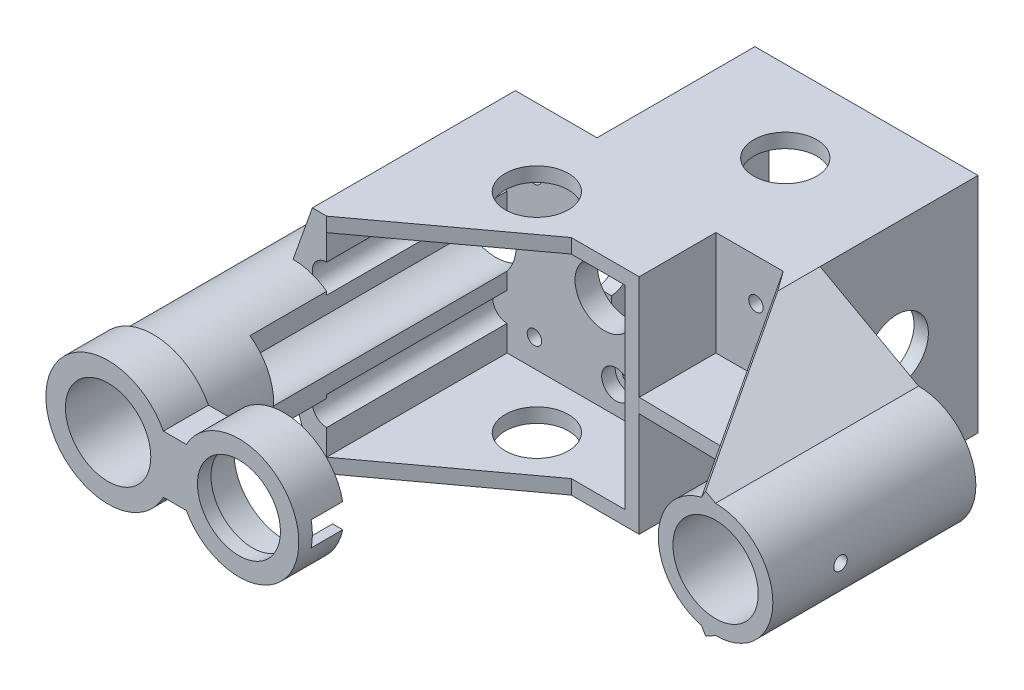
SolidWorks part; units mm, degrees
material "Pure Gold"
ref_plane "Front" through (0, 0, 0) normal (0, 0, 1) x (1, 0, 0)
ref_plane "Top" through (0, 0, 0) normal (0, 1, 0) x (1, 0, 0)
ref_plane "Right" through (0, 0, 0) normal (1, 0, 0) x (0, 0, -1)
sketch "Sketch4" plane through (0, 0, 0) normal (0, 0, 1) x (1, 0, 0)
  line L0 (0, -42.8625) -> (0, 41.275) construction
  line L1 (-49.15, -15.5) -> (-80.15, 15.5) construction
  line L2 (-80.15, -15.5) -> (-49.15, 15.5) construction
  line L3 (-39.925, 44.5615) -> (-39.925, -66.5635) construction
  line L4 (-71.275, 44.5615) -> (-71.275, -66.5635) construction
  line L8 (-62.05, 15.5) -> (-31.05, -15.5) construction
  line L9 (-31.05, 15.5) -> (-62.05, -15.5) construction
  line L11 (-31.05, 36.624) -> (-31.05, -53.8635) construction
  line L12 (43.75, 0) -> (-164.4633, 0) construction
  line L13 (-62.05, 36.624) -> (-62.05, -53.8635) construction
  line L14 (-49.15, 36.624) -> (-49.15, -53.8635) construction
  line L15 (-80.15, 36.624) -> (-80.15, -53.8635) construction
  line L16 (-113.2228, 15.5) -> (-0.2036, 15.5) construction
  line L17 (-113.2228, -15.5) -> (-0.2036, -15.5) construction
  line L18 (-25, -66.5635) -> (-25, 44.5615) construction
  line L19 (-68.1, -66.5635) -> (-68.1, 44.5615) construction
  line L20 (-43.1, 44.5615) -> (-43.1, -66.5635) construction
  line L21 (-86.2, -66.5635) -> (-86.2, 44.5615) construction
  line L22 (5.8397, -21.55) -> (-134.1626, -21.55) construction
  line L23 (5.8397, 21.55) -> (-134.1626, 21.55) construction
  line L24 (10.9249, -24.725) -> (-138.6228, -24.725) construction
  line L25 (10.9249, 24.725) -> (-138.6228, 24.725) construction
  line L26 (-89.375, 44.5615) -> (-89.375, -66.5635) construction
  line L27 (-21.825, 44.5615) -> (-21.825, -66.5635) construction
  circle A0 centre (0, 0) radius 12.7 construction
  circle A1 centre (0, 0) radius 15.875 construction
  circle A2 centre (0, 0) radius 9.46 construction
  circle A3 centre (-93.65, 0) radius 9.46 construction
  arc A4 (-93.65, 12.7) -> (-93.65, -12.7) centre (-93.65, 0) ccw construction
  circle A5 centre (27.27, 0) radius 9.46 construction
  circle A6 centre (27.27, 0) radius 12.7 construction
  circle A7 centre (-120.3675, 0) radius 9.46 construction
  circle A8 centre (-120.3675, 0) radius 12.7 construction
  point P3 (0, 0)
  point P6 (-49.15, -15.5)
  point P11 (-93.65, 0)
  point P12 (-49.15, 15.5)
  point P13 (-46.55, 0)
  point P14 (-80.15, 15.5)
  point P15 (-80.15, -15.5)
  point P61 (-64.65, 0)
  point P65 (27.27, 0)
  point P66 (-120.3675, 0)
  dimension "D20" = 3.175
  dimension "D18" = 29
  dimension "D26" = 73.82
  dimension "D27" = 64.65
  dimension "D2" = 31
  dimension "D3" = 25
  dimension "D4" = 31
  dimension "D5" = 21.825
  dimension "D6" = 15.5
  dimension "D7" = 15.5
  dimension "D8" = 6.05
  dimension "D9" = 6.05
  dimension "D10" = 6.05
  dimension "D11" = 6.05
  dimension "D12" = 6.05
  dimension "D13" = 6.05
  dimension "D14" = 3.175
  dimension "D15" = 3.175
  dimension "D16" = 3.175
  dimension "D17" = 3.175
  dimension "D19" = 3.175
  dimension "D21" = 3.175
  dimension "D22" = 46.55
  dimension "D23" = 47.1
  dimension "D24" = 58.32
  dimension "D25" = 147.6375
sketch "Sketch5" plane through (0, 0, 0) normal (0, 0, 1) x (1, 0, 0)
  line L0 (-21.825, -24.725) -> (0, -12.7)
  line L1 (10.9249, -24.725) -> (-138.6228, -24.725) construction
  line L2 (-21.825, 44.5615) -> (-21.825, -66.5635) construction
  line L3 (0, -42.8625) -> (0, 41.275) construction
  line L4 (10.9249, 24.725) -> (-138.6228, 24.725) construction
  line L5 (-21.825, 24.725) -> (0, 12.7)
  line L6 (-93.65, 0) -> (-93.65, -30.9694) construction
  line L7 (-93.65, 12.7) -> (-89.375, 24.725)
  line L8 (-89.375, 44.5615) -> (-89.375, -66.5635) construction
  line L9 (-89.375, 24.725) -> (-21.825, 24.725)
  line L10 (-89.375, -24.725) -> (-93.65, -12.7)
  line L11 (-89.375, -24.725) -> (-21.825, -24.725)
  circle A0 centre (0, 0) radius 12.7 construction
  arc A1 (0, 12.7) -> (0, -12.7) centre (0, 0) cw
  circle A2 centre (0, 0) radius 9.46
  circle A3 centre (-93.65, 0) radius 9.46
  arc A4 (-93.65, 12.7) -> (-93.65, -12.7) centre (-93.65, 0) ccw
  circle A6 centre (-31.05, 15.5) radius 1.6
  circle A7 centre (-31.05, -15.5) radius 1.6
  circle A8 centre (-49.15, -15.5) radius 1.6
  circle A9 centre (-49.15, 15.5) radius 1.6
  circle A10 centre (-62.05, 15.5) radius 1.6
  circle A11 centre (-80.15, 15.5) radius 1.6
  circle A12 centre (-80.15, -15.5) radius 1.6
  circle A13 centre (-62.05, -15.5) radius 1.6
extrude "Extrude1" add sketch "Sketch5" along normal blind 5
sketch "Sketch6" plane through (0, 0, 5) normal (0, 0, 1) x (1, 0, 0)
  line L0 (-86.2, -21.55) -> (-43.1, -21.55)
  line L1 (-86.2, -66.5635) -> (-86.2, 44.5615) construction
  line L2 (5.8397, -21.55) -> (-134.1626, -21.55) construction
  line L3 (-43.1, 44.5615) -> (-43.1, -66.5635) construction
  line L4 (-43.1, -21.55) -> (-43.1, 21.55)
  line L5 (5.8397, 21.55) -> (-134.1626, 21.55) construction
  line L6 (-43.1, 21.55) -> (-86.2, 21.55)
  line L7 (-39.925, 24.725) -> (-89.375, 24.725)
  line L8 (-93.65, -12.7) -> (-89.375, -24.725) construction
  line L9 (-39.925, 44.5615) -> (-39.925, -66.5635) construction
  line L10 (10.9249, 24.725) -> (-138.6228, 24.725) construction
  line L11 (-12.601, 1.5825) -> (-39.925, 1.5825)
  line L12 (-39.925, -24.725) -> (-89.375, -24.725)
  line L13 (-86.2, 21.55) -> (-86.2, 15.8916)
  line L14 (-86.2, -9.5084) -> (-86.2, -5.83)
  line L15 (-89.375, -24.725) -> (-93.65, -12.7)
  line L16 (-89.375, 24.725) -> (-93.65, 12.7)
  line L19 (-86.2, 9.5416) -> (-86.2, 5.83)
  line L20 (-86.2, -21.55) -> (-86.2, -15.8584)
  line L24 (-39.925, -1.5851) -> (-12.6007, -1.5851)
  line L25 (-39.925, 1.5825) -> (-39.925, 24.725)
  line L27 (-21.825, -24.725) -> (0, -12.7)
  line L28 (-21.825, 24.725) -> (0, 12.7)
  line L29 (-25, 24.725) -> (-3.1127, 12.3127)
  line L30 (-25, -66.5635) -> (-25, 44.5615) construction
  line L31 (-25, -24.725) -> (-3.1127, -12.3127)
  line L32 (10.9249, -24.725) -> (-138.6228, -24.725) construction
  line L33 (-25, -24.725) -> (-21.825, -24.725)
  line L34 (-39.925, -1.5851) -> (-39.925, -24.725)
  line L35 (-25, 24.725) -> (-21.825, 24.725)
  line L36 (0, -42.8625) -> (0, 41.275) construction
  circle A0 centre (-93.65, 0) radius 9.46 construction
  arc A1 (-93.65, 12.7) -> (-93.65, -12.7) centre (-93.65, 0) ccw
  arc A3 (-86.2, 5.83) -> (-86.2, -5.83) centre (-93.65, 0) ccw
  circle A4 centre (0, 0) radius 9.46
  circle A5 centre (0, 0) radius 12.7 construction
  arc A6 (0, -12.7) -> (0, 12.7) centre (0, 0) ccw
  arc A7 (-3.1127, 12.3127) -> (-12.601, 1.5825) centre (0, 0) ccw
  arc A8 (-3.1127, -12.3127) -> (-12.6007, -1.5851) centre (0, 0) cw
  circle A13 centre (-86.2, 12.7166) radius 3.175 construction
  circle A14 centre (-86.2, -12.6834) radius 3.175 construction
  arc A15 (-86.2, 15.8916) -> (-86.2, 9.5416) centre (-86.2, 12.7166) ccw
  arc A16 (-86.2, -9.5084) -> (-86.2, -15.8584) centre (-86.2, -12.6834) ccw
  point P36 (-86.2, 12.7166)
  point P39 (-86.2, -12.6834)
extrude "Extrude2" add sketch "Sketch6" along normal blind 40
sketch "Sketch7" plane through (0, 0, 0) normal (0, 0, -1) x (-1, 0, 0)
  line L0 (68.1, 21.55) -> (25, 21.55)
  line L1 (25, -66.5635) -> (25, 44.5615) construction
  line L2 (-5.8397, -21.55) -> (134.1626, -21.55) construction
  line L3 (25, 21.55) -> (25, -21.55)
  line L4 (68.1, -66.5635) -> (68.1, 44.5615) construction
  line L5 (-5.8397, 21.55) -> (134.1626, 21.55) construction
  line L6 (68.1, 21.55) -> (68.1, -21.55)
  line L7 (68.1, -21.55) -> (25, -21.55)
  line L8 (21.825, 24.725) -> (21.825, -24.725)
  line L9 (21.825, 24.725) -> (71.275, 24.725)
  line L10 (71.275, 44.5615) -> (71.275, -66.5635) construction
  line L11 (-10.9249, 24.725) -> (138.6228, 24.725) construction
  line L12 (71.275, 24.725) -> (71.275, -24.725)
  line L13 (-10.9249, -24.725) -> (138.6228, -24.725) construction
  line L14 (71.275, -24.725) -> (21.825, -24.725)
extrude "Extrude3" add sketch "Sketch7" along normal blind 35
sketch "Sketch12" plane through (4.5259, 7.9808, 0) normal (-0.4933, -0.8699, 0) x (0, 0, 1)
  line L0 (45, 8.7814) -> (5, 33.9433)
  line L1 (5, 33.9433) -> (45, 33.9433)
  line L2 (45, 33.9433) -> (45, 8.7814)
extrude "Extrude5" cut sketch "Sketch12" against normal up to surface (1.5323 mm away)
sketch "Sketch13" plane through (4.5259, -7.9808, 0) normal (-0.4933, 0.8699, 0) x (0, 0, 1)
  line L0 (45, -8.7814) -> (5, -33.9433)
  line L1 (5, -33.9433) -> (45, -33.9433)
  line L2 (45, -33.9433) -> (45, -8.7814)
extrude "Extrude6" cut sketch "Sketch13" against normal up to surface (1.5323 mm away)
sketch "Sketch16" plane through (0, -24.725, 0) normal (0, -1, 0) x (1, 0, 0)
  line L0 (-39.925, 5) -> (-39.925, 22) construction
  line L1 (-39.925, 45) -> (-39.925, 5) construction
  line L2 (-39.925, 22) -> (-16.782, 22.4034)
  line L3 (-16.782, 22.4034) -> (-12.6007, 29.0539)
  line L4 (-12.6007, 45) -> (-12.6007, 5) construction
  line L5 (-12.6007, 29.0539) -> (-12.6007, 45)
  line L6 (-12.6007, 45) -> (-86.2, 45)
  line L7 (-86.2, 45) -> (-54.9816, 22)
  line L8 (-54.9816, 22) -> (-39.925, 22)
  line L9 (-46.55, 0) -> (-46.55, -39.1338) construction
  line L10 (-67.6181, 0) -> (-67.6181, 27.6964) construction
  line L11 (10.9249, 0) -> (-138.6228, 0) construction
  circle A0 centre (-46.55, -17) radius 7
  circle A1 centre (-67.6181, 17) radius 7
extrude "Extrude9" cut sketch "Sketch16" against normal up to surface (49.45 mm away) up to face at (-47.67, 24.725, 3.9695)
sketch "Sketch17" plane through (0, 0, 45) normal (0, 0, 1) x (1, 0, 0)
  line L1 (-86.2, -66.5635) -> (-86.2, 44.5615) construction
  line L2 (-86.2, 10.2853) -> (-86.2, 5.83)
  line L3 (-86.2, -5.83) -> (-86.2, -10.2853)
  arc A0 (-86.2, 5.83) -> (-86.2, -5.83) centre (-93.65, 0) ccw
  arc A1 (-93.65, 12.7) -> (-92.406, -12.6389) centre (-93.65, 0) ccw
  arc A2 (-93.65, 12.7) -> (-93.65, -12.7) centre (-93.65, 0) ccw construction
  arc A3 (-92.406, -12.6389) -> (-86.2, -10.2853) centre (-93.65, 0) ccw
  arc A4 (-93.65, 12.7) -> (-86.2, 10.2853) centre (-93.65, 0) cw
extrude "Extrude10" add sketch "Sketch17" along normal blind 17
sketch "Sketch18" plane through (0, 0, 62) normal (0, 0, 1) x (1, 0, 0)
  circle A0 centre (-93.65, 0) radius 9.46
  circle A1 centre (-93.65, 0) radius 12.7
extrude "Extrude11" add sketch "Sketch18" along normal blind 14
sketch "Sketch19" plane through (0, 0, 76) normal (0, 0, 1) x (1, 0, 0)
  line L0 (-81.3983, -6.3446) -> (-76.3158, -6.3446)
  line L1 (-81.3983, 6.3446) -> (-76.3158, 6.3446)
  circle A0 centre (-64.65, 0) radius 11.1
  circle A1 centre (-64.65, 0) radius 13.2795 construction
  circle A2 centre (-93.65, 0) radius 9.46
  circle A3 centre (-93.65, 0) radius 13.797 construction
  arc A4 (-76.3158, -6.3446) -> (-76.3158, 6.3446) centre (-64.65, 0) ccw
  arc A5 (-81.3983, 6.3446) -> (-81.3983, -6.3446) centre (-93.65, 0) ccw
extrude "Extrude12" add sketch "Sketch19" along normal blind 7
sketch "Sketch20" plane through (0, 0, 83) normal (0, 0, 1) x (1, 0, 0)
  line L1 (-81.3983, -6.3446) -> (-76.3158, -6.3446) construction
  line L2 (-81.3983, -6.3446) -> (-76.3158, -6.3446)
  line L3 (-81.3983, 6.3446) -> (-76.3158, 6.3446)
  circle A0 centre (-93.65, 0) radius 9.46
  circle A1 centre (-93.65, 0) radius 12.7 construction
  circle A2 centre (-64.65, 0) radius 14.39 construction
  arc A3 (-81.3983, 6.3446) -> (-81.3983, -6.3446) centre (-93.65, 0) ccw
  arc A4 (-76.3158, -6.3446) -> (-76.3158, 6.3446) centre (-64.65, 0) ccw
  circle A5 centre (-64.65, 0) radius 9.2
extrude "Extrude13" add sketch "Sketch20" along normal blind 3
sketch "Sketch21" plane through (-43.1, 0, 0) normal (-1, 0, 0) x (0, 0, 1)
  line L0 (76, 0) -> (76, -2.7)
  line L1 (76, 13.797) -> (76, -13.797) construction
  line L2 (76, 0) -> (76, 2.7)
  line L3 (76, -2.7) -> (83, -2.7)
  line L4 (83, 11.1) -> (83, -11.1) construction
  line L5 (83, -2.7) -> (83, 2.7)
  line L6 (83, 2.7) -> (76, 2.7)
extrude "Extrude14" cut sketch "Sketch21" along normal blind 15
sketch "Sketch22" plane through (0, 0, 5) normal (0, 0, 1) x (1, 0, 0)
  circle A0 centre (-62.05, 15.5) radius 3.2
  circle A1 centre (-62.05, -15.5) radius 3.2
extrude "Extrude15" cut sketch "Sketch22" against normal blind 3
sketch "Sketch23" plane through (0, 0, 0) normal (0, 0, -1) x (-1, 0, 0)
  circle A0 centre (49.15, 15.5) radius 3.2
  circle A1 centre (49.15, -15.5) radius 3.2
extrude "Extrude16" cut sketch "Sketch23" against normal blind 3
sketch "Sketch24" plane through (-71.275, 0, 0) normal (-1, 0, 0) x (0, 0, 1)
  line L0 (0, 0) -> (0, 4)
  line L1 (0, -66.5635) -> (0, 44.5615) construction
  line L2 (0, 0) -> (0, -4)
  circle A0 centre (-17, 0) radius 7
  arc A1 (0, 4) -> (0, -4) centre (0, 0) ccw
extrude "Extrude17" cut sketch "Sketch24" against normal up to surface (49.45 mm away) up to face at (-21.825, 0, -17.5)
sketch "Sketch25" plane through (0, 0, 0) normal (0, 0, -1) x (-1, 0, 0)
  circle A0 centre (46.55, 0) radius 6.5
  circle A1 centre (64.65, 0) radius 6.5
extrude "Extrude18" cut sketch "Sketch25" against normal up to surface (5 mm away) up to face at (-58.85, -15.5, 5)
sketch "Sketch26" plane through (-12.6007, 0, 0) normal (-1, 0, 0) x (0, 0, 1)
  line L1 (30, 39.8112) -> (30, -51.0479) construction
  line L2 (0, 44.5615) -> (0, -66.5635) construction
  circle A0 centre (30, 0) radius 1.5
  dimension "D1" = 30
extrude "Extrude19" cut sketch "Sketch26" against normal up to surface and the other way up to surface
